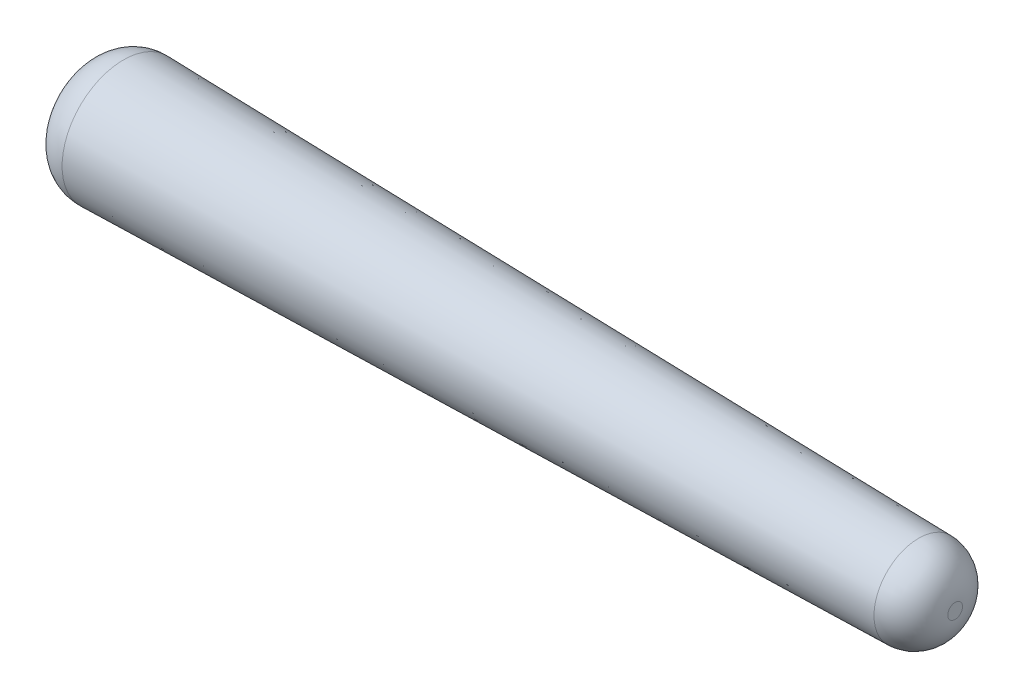
SolidWorks part; units mm, degrees
ref_plane "Front Plane" through (0, 0, 0) normal (0, 0, 1) x (1, 0, 0)
ref_plane "Top Plane" through (0, 0, 0) normal (0, 1, 0) x (1, 0, 0)
ref_plane "Right Plane" through (0, 0, 0) normal (1, 0, 0) x (0, 0, -1)
sketch "Sketch1" plane through (0, 0, 0) normal (0, 0, 1) x (1, 0, 0)
  line L0 (-3.5, 0) -> (3.5, 0) construction
  line L1 (0, 0) -> (55, 0) construction
  circle A0 centre (0, 0) radius 3.5 construction
ref_plane "Plane1" through (-3.5, 0, 0) normal (1, 0, 0) x (0, 0, -1)
sketch "Sketch2" plane through (-3.5, 0, 0) normal (1, 0, 0) x (0, 0, -1)
  circle A0 centre (0, 0) radius 0.5
  dimension "D1" = 1
extrude "Boss-Extrude1" add sketch "Sketch2" along normal up to vertex (7 mm away) draft 1.2 up to point (3.5, 0, 0)
fillet "Fillet1" radius 0.3 2 edges at (-3.5, 0, -0.5) (3.5, 0, -0.3534)
